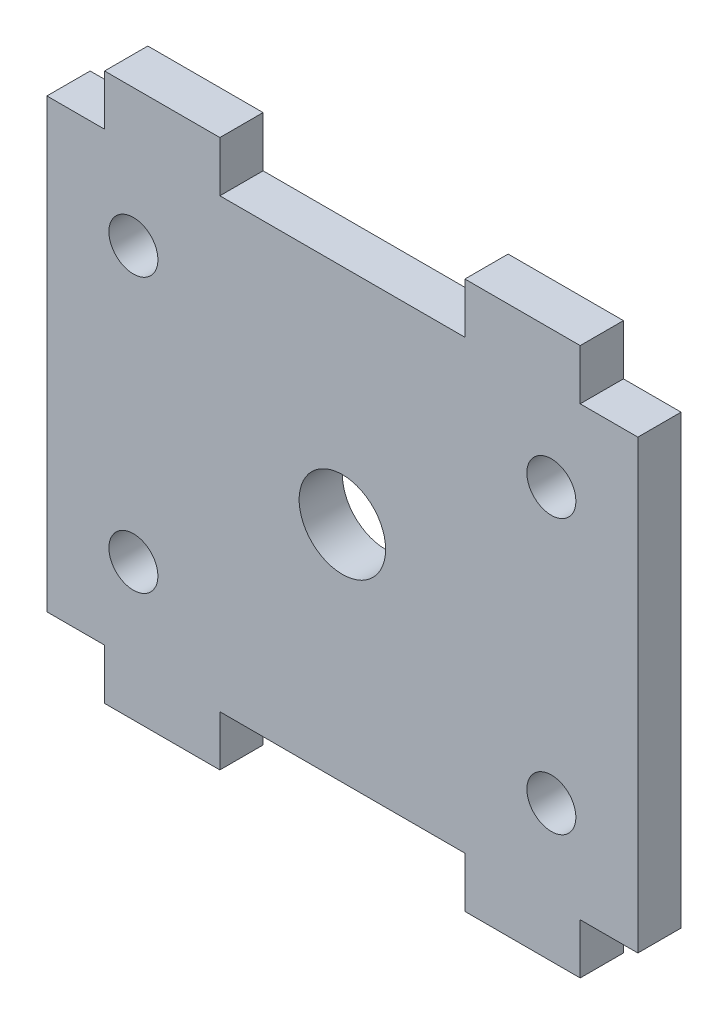
SolidWorks part; units mm, degrees
ref_plane "Front Plane" through (0, 0, 0) normal (0, 0, 1) x (1, 0, 0)
ref_plane "Top Plane" through (0, 0, 0) normal (0, 1, 0) x (1, 0, 0)
ref_plane "Right Plane" through (0, 0, 0) normal (1, 0, 0) x (0, 0, -1)
sketch "Sketch1" plane through (0, 0, 0) normal (0, 0, 1) x (1, 0, 0)
  line L0 (20.5, -15.5) -> (20.5, 15.5)
  line L1 (20.5, 15.5) -> (16.5, 15.5)
  line L2 (16.5, 15.5) -> (16.5, 19)
  line L3 (16.5, 19) -> (8.5, 19)
  line L4 (8.5, 19) -> (8.5, 15.5)
  line L5 (8.5, 15.5) -> (-8.5, 15.5)
  line L8 (8.5, -15.5) -> (-8.5, -15.5)
  line L9 (8.5, -19) -> (8.5, -15.5)
  line L10 (16.5, -19) -> (8.5, -19)
  line L11 (16.5, -15.5) -> (16.5, -19)
  line L12 (20.5, -15.5) -> (16.5, -15.5)
  line L13 (-20.5, -15.5) -> (-16.5, -15.5)
  line L14 (-16.5, -15.5) -> (-16.5, -19)
  line L15 (-16.5, -19) -> (-8.5, -19)
  line L16 (-8.5, -19) -> (-8.5, -15.5)
  line L18 (-8.5, 19) -> (-8.5, 15.5)
  line L19 (-16.5, 19) -> (-8.5, 19)
  line L20 (-16.5, 15.5) -> (-16.5, 19)
  line L21 (-20.5, 15.5) -> (-16.5, 15.5)
  line L22 (-20.5, -15.5) -> (-20.5, 15.5)
  circle A0 centre (0, 0) radius 3.5
  point P24 (0, -15.5)
  dimension "D3" = 8
  dimension "D4" = 4
  dimension "D6" = 3.5
extrude "Boss-Extrude1" add sketch "Sketch1" along normal blind 3 contours L21 L20 L19 L18 L5 L4 L3 L2 L1 L0 L12 L11 L10 L9 L8 L16 L15 L14 L13 L22
hole_wizard "Ø6.0 (6) Diameter Hole1" positions "Sketch3" profile "Sketch2" hole size "Ø6.0" standard "ISO" end condition up to next
sketch "Sketch3" plane through (0, 0, 3) normal (0, 0, 1) x (1, 0, 0)
  point P0 (0, 0)
sketch "Sketch2" plane through (0, 0, 3) normal (1, 0, 0) x (0, -1, 0)
  line L0 (0, 0) -> (0, 3)
  line L1 (0, 3) -> (3, 3)
  line L2 (3, 3) -> (3, 0)
  line L5 (3, 0) -> (0, 0)
  line L11 (0, -6.35) -> (0, 107.95) construction
  dimension "Thru Hole Dia." = 6
  dimension "Thru Hole Depth" = 3
hole_wizard "M3 Clearance Hole1" positions "Sketch5" profile "Sketch4" hole size "M3" standard "ISO" end condition up to next
sketch "Sketch5" plane through (0, 0, 3) normal (0, 0, 1) x (1, 0, 0)
  line L0 (20.5, 15.5) -> (16.5, 15.5) construction
  line L1 (20.5, -15.5) -> (20.5, 15.5) construction
  point P0 (14.5, 9.5)
  dimension "D1" = 6
  dimension "D2" = 6
sketch "Sketch4" plane through (14.5, 9.5, 3) normal (1, 0, 0) x (0, -1, 0)
  line L0 (0, 0) -> (0, 3.001)
  line L1 (0, 3.001) -> (1.7, 3.001)
  line L2 (1.7, 3.001) -> (1.7, 0)
  line L5 (1.7, 0) -> (0, 0)
  line L11 (0, -6.35) -> (0, 107.95) construction
  dimension "Thru Hole Dia." = 3.4
  dimension "Thru Hole Depth" = 3.001
mirror "Mirror1" about plane through (0, 0, 0) normal (1, 0, 0) of "M3 Clearance Hole1"
mirror "Mirror2" about plane through (0, 0, 0) normal (0, 1, 0) of "Mirror1", "M3 Clearance Hole1"
